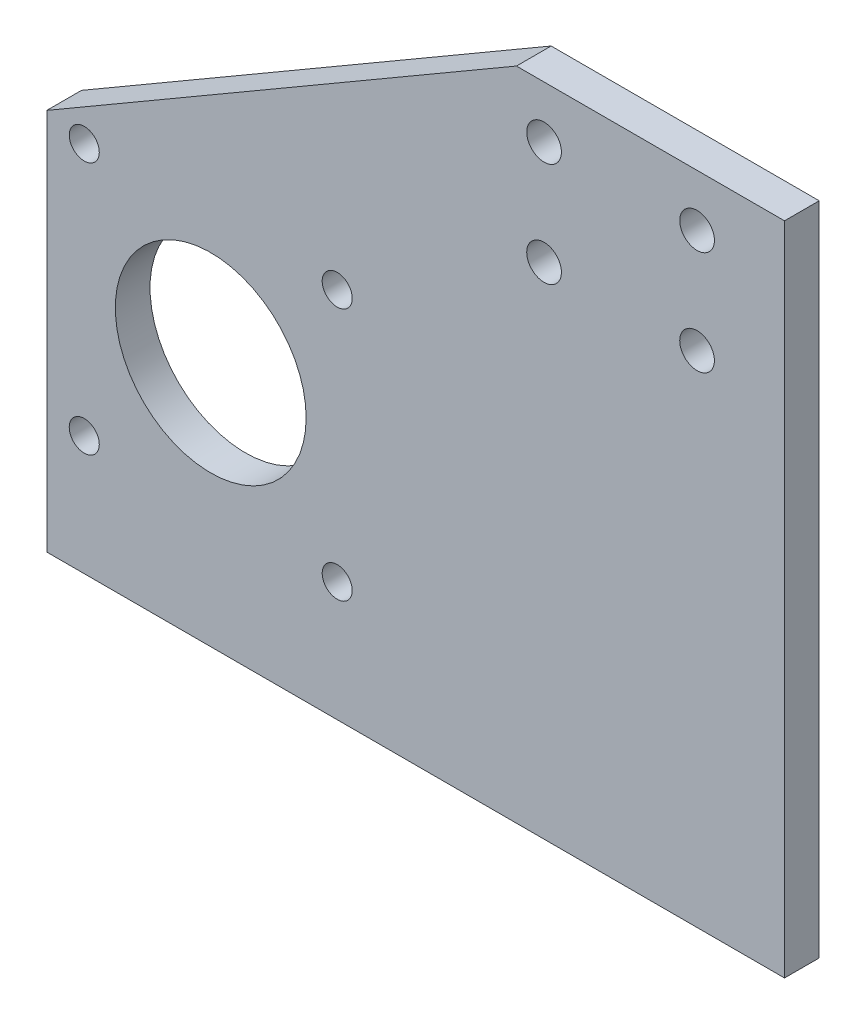
SolidWorks part; units mm, degrees
material "Acero al carbono no aleado"
ref_plane "Alzado" through (0, 0, 0) normal (0, 0, 1) x (1, 0, 0)
ref_plane "Planta" through (0, 0, 0) normal (0, 1, 0) x (1, 0, 0)
ref_plane "Vista lateral" through (0, 0, 0) normal (1, 0, 0) x (0, 0, -1)
sketch "Croquis1" plane through (0, 0, 0) normal (0, 0, 1) x (1, 0, 0)
  line L0 (-135, 70) -> (0, 70) construction
  line L1 (0, 0) -> (-135, 0)
  line L2 (0, 0) -> (0, 120)
  line L3 (0, 120) -> (-49.0561, 120)
  line L4 (-135, 0) -> (-135, 70)
  line L5 (-140.1813, 100.95) -> (9.4988, 100.95) construction
  line L6 (-60, 148.9102) -> (-60, 117.1882) construction
  line L7 (-62.7594, 110.475) -> (6.3776, 110.475) construction
  line L9 (-135, 70) -> (-49.0561, 120)
  circle A0 centre (-44, 110.475) radius 3.175
  circle A1 centre (-16, 110.475) radius 3.175
  circle A2 centre (-16, 91.425) radius 3.175
  circle A3 centre (-44, 91.425) radius 3.175
  dimension "D7" = 16
  dimension "D1" = 135
  dimension "D2" = 120
  dimension "D3" = 50
  dimension "D4" = 19.05
  dimension "D5" = 60
  dimension "D6" = 19.05
  dimension "D8" = 16
extrude "Saliente-Extruir1" add sketch "Croquis1" along normal blind 6.35
sketch "Croquis2" plane through (0, 0, 6.35) normal (0, 0, 1) x (1, 0, 0)
  line L0 (-105, 126.4955) -> (-105, -10.042) construction
  line L1 (-155.1031, 45) -> (14.7181, 45) construction
  line L2 (0, 120) -> (-49.0561, 120) construction
  line L3 (-157.9676, 68.15) -> (11.8273, 68.15) construction
  line L5 (-135, 70) -> (-135, 0) construction
  line L6 (-138.0031, 70) -> (5.5508, 70) construction
  circle A1 centre (-128.145, 68.15) radius 2.75
  circle A2 centre (-128.145, 21.85) radius 2.75
  circle A3 centre (-81.855, 21.85) radius 2.75
  circle A4 centre (-81.855, 68.15) radius 2.75
  circle A5 centre (-105, 45) radius 17.4625
  dimension "D5" = 5.5
  dimension "D1" = 75
  dimension "D2" = 30
  dimension "D3" = 23.145
  dimension "D4" = 23.15
  dimension "D6" = 50
extrude "Cortar-Extruir1" cut sketch "Croquis2" against normal blind 12.7
